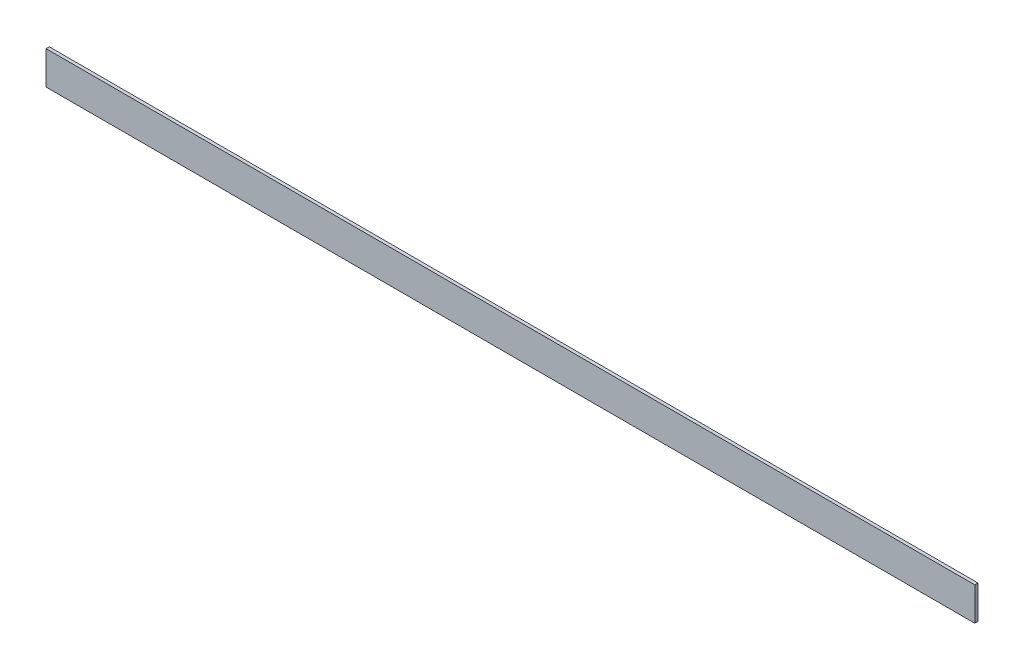
SolidWorks part; units mm, degrees
ref_plane "Front Plane" through (0, 0, 0) normal (0, 0, 1) x (1, 0, 0)
ref_plane "Top Plane" through (0, 0, 0) normal (0, 1, 0) x (1, 0, 0)
ref_plane "Right Plane" through (0, 0, 0) normal (1, 0, 0) x (0, 0, -1)
sketch "Sketch1" plane through (0, 0, 0) normal (0, 0, 1) x (1, 0, 0)
  line L1 (0, 0) -> (920.75, 0)
  line L2 (0, 0) -> (0, 33)
  line L3 (0, 33) -> (920.75, 33)
  line L4 (920.75, 0) -> (920.75, 33)
  dimension "D1" = 33
  dimension "D2" = 920.75
extrude "Boss-Extrude1" add sketch "Sketch1" along normal blind 3.175
